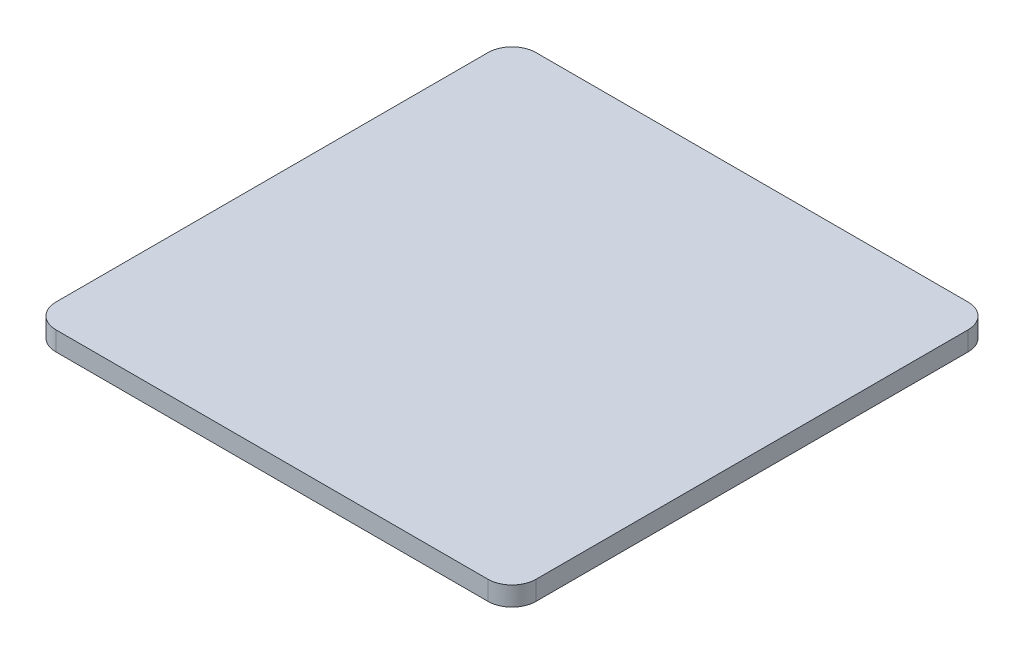
SolidWorks part; units mm, degrees
ref_plane "Front Plane" through (0, 0, 0) normal (0, 0, 1) x (1, 0, 0)
ref_plane "Top Plane" through (0, 0, 0) normal (0, 1, 0) x (1, 0, 0)
ref_plane "Right Plane" through (0, 0, 0) normal (1, 0, 0) x (0, 0, -1)
sketch "Sketch1" plane through (0, 0, 0) normal (0, 1, 0) x (1, 0, 0)
  line L1 (-50, 50) -> (50, 50)
  line L2 (-50, 50) -> (-50, -50)
  line L3 (-50, -50) -> (50, -50)
  line L4 (50, 50) -> (50, -50)
  line L5 (-50, 50) -> (50, -50) construction
  line L6 (-50, -50) -> (50, 50) construction
  point P0 (0, 0)
  dimension "D1" = 100
  dimension "D2" = 100
extrude "Boss-Extrude1" add sketch "Sketch1" along normal blind 4
fillet "Fillet1" radius 5 4 edges at (50, 2, 50) (-50, 2, -50) (50, 2, -50) (-50, 2, 50)
